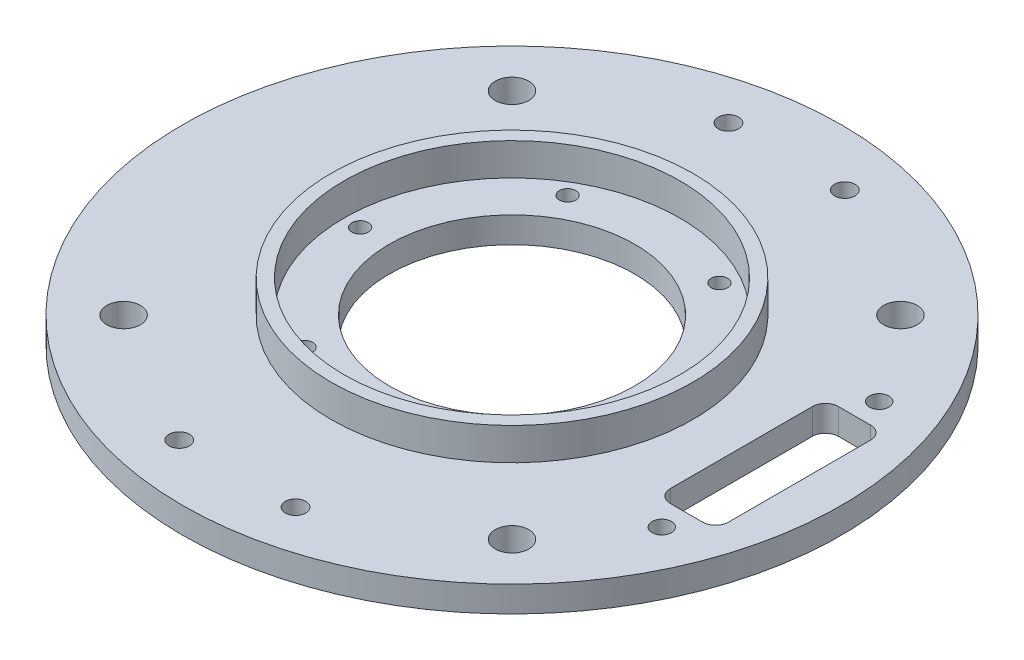
SolidWorks part; units mm, degrees
material "1060 Сплав"
ref_plane "Спереди" through (0, 0, 0) normal (0, 0, 1) x (1, 0, 0)
ref_plane "Сверху" through (0, 0, 0) normal (0, 1, 0) x (1, 0, 0)
ref_plane "Справа" through (0, 0, 0) normal (1, 0, 0) x (0, 0, -1)
sketch "Эскиз1" plane through (0, 0, 0) normal (0, 1, 0) x (1, 0, 0)
  circle A0 centre (0, 0) radius 19
  circle A1 centre (0, 0) radius 51
  dimension "D1" = 38
  dimension "D2" = 102
extrude "Бобышка-Вытянуть1" add sketch "Эскиз1" along normal blind 4
hole_wizard "Сверло под метчик  спиральное M2.51" positions "Эскиз2" profile "Эскиз3" hole size "M2.5x0.45" standard "DIN"
sketch "Эскиз2" plane through (0, 4, 0) normal (0, 1, 0) x (1, 0, 0)
  point P0 (23.5, 0)
  dimension "D1" = 23.5
sketch "Эскиз3" plane through (23.5, 4, 0) normal (1, 0, 0) x (0, 0, 1)
  line L0 (0, 0) -> (0, 8.7661)
  line L1 (0, 8.7661) -> (1.275, 8)
  line L2 (1.275, 8) -> (1.275, 0)
  line L5 (1.275, 0) -> (0, 0)
  line L10 (0, 8.7661) -> (-1.275, 8) construction
  line L11 (0, -6.35) -> (0, 107.95) construction
  dimension "Диаметр отверстия" = 2.55
  dimension "Глубина отверстия" = 8
  dimension "Угол заточки сверла" = 118
pattern_circular "Круговой массив1" count 6 over 360 about axis through (0, 0, 0) along (0, 1, 0) of "Сверло под метчик  спиральное M2.51"
hole_wizard "Сверло под метчик  спиральное M32" positions "Эскиз4" profile "Эскиз5" hole size "M3x0.5" standard "DIN" end condition through all
sketch "Эскиз4" plane through (0, 0, 0) normal (0, -1, 0) x (-1, 0, 0)
  point P0 (-9, -42.5)
  dimension "D1" = 9
  dimension "D2" = 42.5
sketch "Эскиз5" plane through (9, 0, 42.5) normal (1, 0, 0) x (0, 0, -1)
  line L0 (0, 0) -> (0, 4)
  line L1 (0, 4) -> (1.575, 4)
  line L2 (1.575, 4) -> (1.575, 0)
  line L5 (1.575, 0) -> (0, 0)
  line L11 (0, -6.35) -> (0, 107.95) construction
  dimension "Диаметр сквозного отверстия" = 3.15
  dimension "Глубина сквозного отверстия" = 4
sketch "Эскиз6" plane through (0, 0, 0) normal (0, 1, 0) x (1, 0, 0)
  line L0 (0, 0) -> (0, 15.2777) construction
  line L1 (0, 0) -> (-12.2514, 0) construction
pattern_linear "Линейный массив1" count 2 spacing 18 along (-1, 0, 0) count 2 spacing 85 along (0, 0, -1) of "Сверло под метчик  спиральное M32"
sketch "Эскиз14" plane through (0, 4, 0) normal (0, 1, 0) x (1, 0, 0)
  circle A0 centre (0, 0) radius 26
  circle A1 centre (0, 0) radius 28
  dimension "D1" = 52
  dimension "D2" = 56
extrude "Бобышка-Вытянуть2" add sketch "Эскиз14" along normal blind 5
sketch "Эскиз16" plane through (0, 4, 0) normal (0, 1, 0) x (1, 0, 0)
  line L0 (0, 0) -> (47.3, 0) construction
  line L2 (44.5, -13) -> (35.5, -13)
  line L3 (44.5, -13) -> (44.5, 13)
  line L4 (44.5, 13) -> (35.5, 13)
  line L5 (35.5, -13) -> (35.5, 13)
  line L6 (44.5, -13) -> (35.5, 13) construction
  line L7 (44.5, 13) -> (35.5, -13) construction
  circle A0 centre (40, 16.82) radius 1.5
  circle A1 centre (40, -16.82) radius 1.5
  point P3 (40, 0)
  dimension "D4" = 3
  dimension "D5" = 3
  dimension "D1" = 40
  dimension "D2" = 9
  dimension "D3" = 26
  dimension "D6" = 16.82
  dimension "D7" = 33.64
extrude "Вырез-Вытянуть1" cut sketch "Эскиз16" against normal through all
fillet "Скругление1" radius 2 4 edges at (44.5, 2, 13) (35.5, 2, 13) (44.5, 2, -13) (35.5, 2, -13)
hole_wizard "Сверло под метчик  спиральное M51" positions "Эскиз17" profile "Эскиз18" hole size "M5x0.8" standard "DIN"
sketch "Эскиз17" plane through (0, 4, 0) normal (0, 1, 0) x (1, 0, 0)
  line L0 (57.5066, 0) -> (-73.8438, 0) construction
  line L2 (0, 59.3684) -> (0, -58.4898) construction
  line L3 (0, 0) -> (-30.052, 30.052) construction
  circle A0 centre (0, 0) radius 42.5
  point P0 (-30.052, 30.052)
  dimension "D1" = 85
  dimension "D2" = 45
sketch "Эскиз18" plane through (-30.052, 4, -30.052) normal (1, 0, 0) x (0, 0, 1)
  line L0 (0, 0) -> (0, 9.5622)
  line L1 (0, 9.5622) -> (2.6, 8)
  line L2 (2.6, 8) -> (2.6, 0)
  line L5 (2.6, 0) -> (0, 0)
  line L10 (0, 9.5622) -> (-2.6, 8) construction
  line L11 (0, -6.35) -> (0, 107.95) construction
  dimension "Диаметр отверстия" = 5.2
  dimension "Глубина отверстия" = 8
  dimension "Угол заточки сверла" = 118
pattern_circular "Круговой массив2" count 4 over 360 about axis through (0, 0, 0) along (0, 1, 0) of "Сверло под метчик  спиральное M51"
